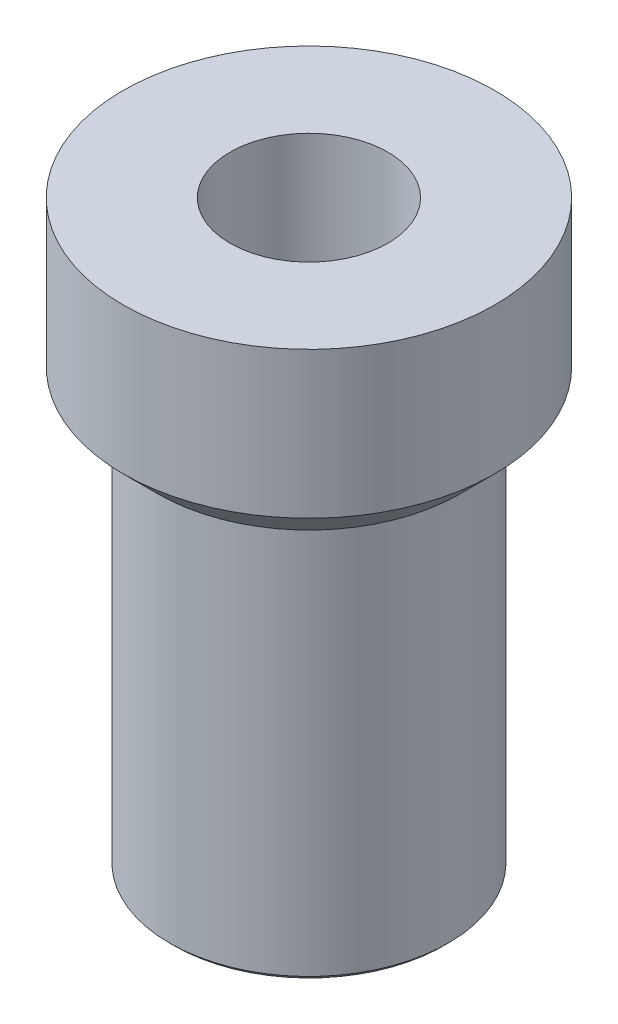
SolidWorks part; units mm, degrees
material "Alloy Steel"
ref_plane "Front Plane" through (0, 0, 0) normal (0, 0, 1) x (1, 0, 0)
ref_plane "Top Plane" through (0, 0, 0) normal (0, 1, 0) x (1, 0, 0)
ref_plane "Right Plane" through (0, 0, 0) normal (1, 0, 0) x (0, 0, -1)
sketch "Sketch1" plane through (0, 0, 0) normal (0, 0, 1) x (1, 0, 0)
  line L0 (0, 31.0566) -> (0, -31.0566) construction
  line L3 (-6, 23.2566) -> (-6, 6.2566)
  line L4 (-5.8, 6.0566) -> (0, 6.0566)
  line L8 (-8, 31.0566) -> (-8, 24.7566)
  line L9 (-6.5, 23.2566) -> (-6, 23.2566)
  line L10 (-8, 31.0566) -> (0, 31.0566)
  line L11 (-6, 6.2566) -> (-5.8, 6.0566)
  line L12 (-8, 24.7566) -> (-6.5, 23.2566)
  line L13 (0, 31.0566) -> (0, 6.0566)
  point P4 (0, 0)
  point P9 (-6, 6.0566)
  point P12 (-8, 23.2566)
  dimension "D1" = 62.1132
  dimension "D2" = 25
  dimension "D4" = 12
  dimension "D5" = 17
  dimension "D6" = 16
revolve "Revolve1" add sketch "Sketch1" angle 360 about L0
sketch "Sketch2" plane through (0, 31.0566, 0) normal (0, 1, 0) x (1, 0, 0)
  point P0 (0, 0)
hole_wizard "M8x1.25 Tapped Hole1" positions "3DSketch1" profile "Sketch3" tap size "M8x1.25" standard "ANSI Metric" end condition through all
sketch3d "3DSketch1"
  point P0 (0, 0, 0)
  point P3 (0, 0, 0)
  point P6 (0, 31.0566, 0)
sketch "Sketch3" plane through (0, 31.0566, 0) normal (1, 0, 0) x (0, 0, 1)
  line L0 (0, 0) -> (0, 25)
  line L1 (0, 25) -> (3.4, 25)
  line L2 (3.4, 25) -> (3.4, 0)
  line L5 (3.4, 0) -> (0, 0)
  line L11 (0, -6.35) -> (0, 107.95) construction
  dimension "Thru Tap Drill Dia." = 6.8
  dimension "Thru Tap Drill Depth" = 25
